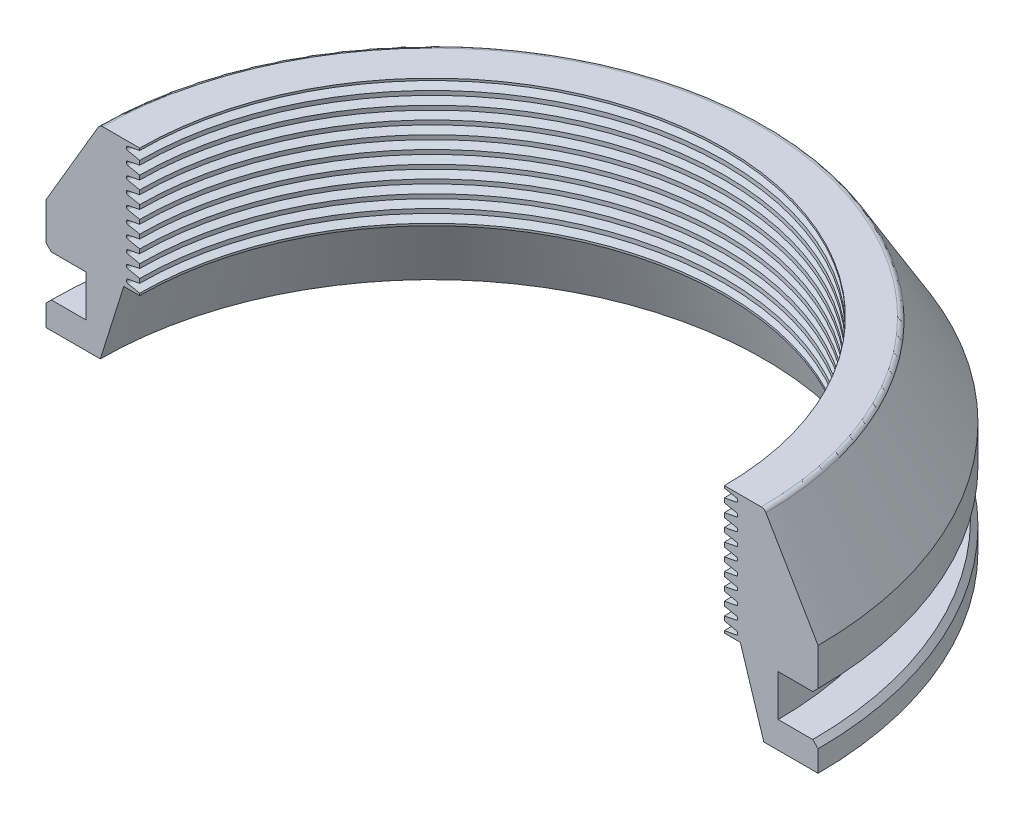
SolidWorks part; units mm, degrees
material "1060 Alloy"
ref_plane "Front Plane" through (0, 0, 0) normal (0, 0, 1) x (1, 0, 0)
ref_plane "Top Plane" through (0, 0, 0) normal (0, 1, 0) x (1, 0, 0)
ref_plane "Right Plane" through (0, 0, 0) normal (1, 0, 0) x (0, 0, -1)
sketch "Sketch2" plane through (0, 0, 0) normal (0, 0, 1) x (1, 0, 0)
  line L0 (0, 0) -> (0, 6.35)
  line L1 (0, 6.35) -> (9.525, 6.35)
  line L2 (9.525, 6.35) -> (9.525, 16.256)
  line L3 (9.525, 16.256) -> (0, 16.256)
  line L4 (0, 16.256) -> (0, 26.416)
  line L5 (0, 26.416) -> (12.827, 48.26)
  line L6 (12.827, 48.26) -> (22.352, 48.26)
  line L7 (22.352, 48.26) -> (22.352, 17.78)
  line L8 (0, 0) -> (184.15, 0) construction
  line L9 (12.954, 0) -> (0, 0)
  line L10 (22.352, 17.78) -> (18.542, 17.78)
  line L11 (18.542, 17.78) -> (12.954, 0)
  line L12 (92.075, 0) -> (92.075, 79.1772) construction
  point P3 (92.075, 0)
  dimension "D1" = 6.35
  dimension "D2" = 48.26
  dimension "D3" = 12.954
  dimension "D4" = 30.48
  dimension "D5" = 22.352
  dimension "D6" = 9.906
  dimension "D7" = 9.525
  dimension "D8" = 3.81
  dimension "D9" = 10.16
  dimension "D10" = 9.525
  dimension "D11" = 184.15
revolve "Revolve1" add sketch "Sketch2" angle 180 about L12
chamfer "Chamfer1" distance 1.27 angle 45 2 edges at (92.075, 16.256, -92.075) (92.075, 6.35, -92.075)
fillet "Fillet1" radius 1.27 1 edges at (92.075, 48.26, -79.248)
sketch "Sketch3" plane through (0, 0, 0) normal (0, 0, 1) x (1, 0, 0)
  line L0 (22.352, 48.26) -> (22.352, 47.752)
  line L1 (22.352, 17.78) -> (22.352, 48.26) construction
  line L2 (22.352, 47.752) -> (19.4833, 47.1783)
  line L3 (19.177, 46.8047) -> (19.177, 46.6673)
  line L4 (19.4833, 46.2937) -> (22.352, 45.72)
  line L5 (22.352, 45.72) -> (22.352, 45.212)
  line L6 (19.177, 46.736) -> (22.352, 46.736) construction
  line L7 (22.352, 47.752) -> (22.352, 45.72)
  line L8 (22.352, 44.704) -> (19.4833, 44.1303)
  line L9 (19.4833, 43.2457) -> (22.352, 42.672)
  line L10 (22.352, 42.672) -> (22.352, 42.164)
  line L11 (19.177, 43.7567) -> (19.177, 43.6193)
  line L12 (22.352, 45.212) -> (22.352, 44.704)
  line L13 (22.352, 41.656) -> (19.4833, 41.0823)
  line L14 (19.4833, 40.1977) -> (22.352, 39.624)
  line L15 (22.352, 39.624) -> (22.352, 39.116)
  line L16 (19.177, 40.7087) -> (19.177, 40.5713)
  line L17 (22.352, 42.164) -> (22.352, 41.656)
  line L18 (22.352, 38.608) -> (19.4833, 38.0343)
  line L19 (19.4833, 37.1497) -> (22.352, 36.576)
  line L20 (22.352, 36.576) -> (22.352, 36.068)
  line L21 (19.177, 37.6607) -> (19.177, 37.5233)
  line L22 (22.352, 39.116) -> (22.352, 38.608)
  line L23 (22.352, 35.56) -> (19.4833, 34.9863)
  line L24 (19.4833, 34.1017) -> (22.352, 33.528)
  line L25 (22.352, 33.528) -> (22.352, 33.02)
  line L26 (19.177, 34.6127) -> (19.177, 34.4753)
  line L27 (22.352, 36.068) -> (22.352, 35.56)
  line L28 (22.352, 32.512) -> (19.4833, 31.9383)
  line L29 (19.4833, 31.0537) -> (22.352, 30.48)
  line L30 (22.352, 30.48) -> (22.352, 29.972)
  line L31 (19.177, 31.5647) -> (19.177, 31.4273)
  line L32 (22.352, 33.02) -> (22.352, 32.512)
  line L33 (22.352, 29.464) -> (19.4833, 28.8903)
  line L34 (19.4833, 28.0057) -> (22.352, 27.432)
  line L35 (22.352, 27.432) -> (22.352, 26.924)
  line L36 (19.177, 28.5167) -> (19.177, 28.3793)
  line L37 (22.352, 29.972) -> (22.352, 29.464)
  line L38 (22.352, 26.416) -> (19.4833, 25.8423)
  line L39 (19.4833, 24.9577) -> (22.352, 24.384)
  line L40 (22.352, 24.384) -> (22.352, 23.876)
  line L41 (19.177, 25.4687) -> (19.177, 25.3313)
  line L42 (22.352, 26.924) -> (22.352, 26.416)
  line L43 (22.352, 23.368) -> (19.4833, 22.7943)
  line L44 (19.4833, 21.9097) -> (22.352, 21.336)
  line L45 (22.352, 21.336) -> (22.352, 20.828)
  line L46 (19.177, 22.4207) -> (19.177, 22.2833)
  line L47 (22.352, 23.876) -> (22.352, 23.368)
  line L48 (22.352, 20.32) -> (19.4833, 19.7463)
  line L49 (19.4833, 18.8617) -> (22.352, 18.288)
  line L50 (22.352, 18.288) -> (22.352, 17.78)
  line L51 (19.177, 19.3727) -> (19.177, 19.2353)
  line L52 (22.352, 20.828) -> (22.352, 20.32)
  line L54 (22.352, 48.26) -> (13.554, 48.26) construction
  line L55 (0, 0) -> (184.15, 0) construction
  line L56 (92.075, 0) -> (92.075, 69.6404) construction
  arc A0 (19.177, 46.6673) -> (19.4833, 46.2937) centre (19.558, 46.6673) ccw
  arc A1 (19.4833, 47.1783) -> (19.177, 46.8047) centre (19.558, 46.8047) ccw
  arc A2 (19.177, 43.6193) -> (19.4833, 43.2457) centre (19.558, 43.6193) ccw
  arc A3 (19.4833, 44.1303) -> (19.177, 43.7567) centre (19.558, 43.7567) ccw
  arc A4 (19.177, 40.5713) -> (19.4833, 40.1977) centre (19.558, 40.5713) ccw
  arc A5 (19.4833, 41.0823) -> (19.177, 40.7087) centre (19.558, 40.7087) ccw
  arc A6 (19.177, 37.5233) -> (19.4833, 37.1497) centre (19.558, 37.5233) ccw
  arc A7 (19.4833, 38.0343) -> (19.177, 37.6607) centre (19.558, 37.6607) ccw
  arc A8 (19.177, 34.4753) -> (19.4833, 34.1017) centre (19.558, 34.4753) ccw
  arc A9 (19.4833, 34.9863) -> (19.177, 34.6127) centre (19.558, 34.6127) ccw
  arc A10 (19.177, 31.4273) -> (19.4833, 31.0537) centre (19.558, 31.4273) ccw
  arc A11 (19.4833, 31.9383) -> (19.177, 31.5647) centre (19.558, 31.5647) ccw
  arc A12 (19.177, 28.3793) -> (19.4833, 28.0057) centre (19.558, 28.3793) ccw
  arc A13 (19.4833, 28.8903) -> (19.177, 28.5167) centre (19.558, 28.5167) ccw
  arc A14 (19.177, 25.3313) -> (19.4833, 24.9577) centre (19.558, 25.3313) ccw
  arc A15 (19.4833, 25.8423) -> (19.177, 25.4687) centre (19.558, 25.4687) ccw
  arc A16 (19.177, 22.2833) -> (19.4833, 21.9097) centre (19.558, 22.2833) ccw
  arc A17 (19.4833, 22.7943) -> (19.177, 22.4207) centre (19.558, 22.4207) ccw
  arc A18 (19.177, 19.2353) -> (19.4833, 18.8617) centre (19.558, 19.2353) ccw
  arc A19 (19.4833, 19.7463) -> (19.177, 19.3727) centre (19.558, 19.3727) ccw
  point P14 (19.177, 46.355)
  point P17 (19.177, 47.117)
  point P39 (92.075, 0)
  dimension "D7" = 0.381
  dimension "D1" = 3.175
  dimension "D2" = 0.508
  dimension "D3" = 0.508
  dimension "D4" = 3.048
  dimension "D5" = 0.762
  dimension "D6" = 10
  dimension "D8" = 3.556
revolve "Cut-Revolve2" cut sketch "Sketch3" angle 360 about L56
